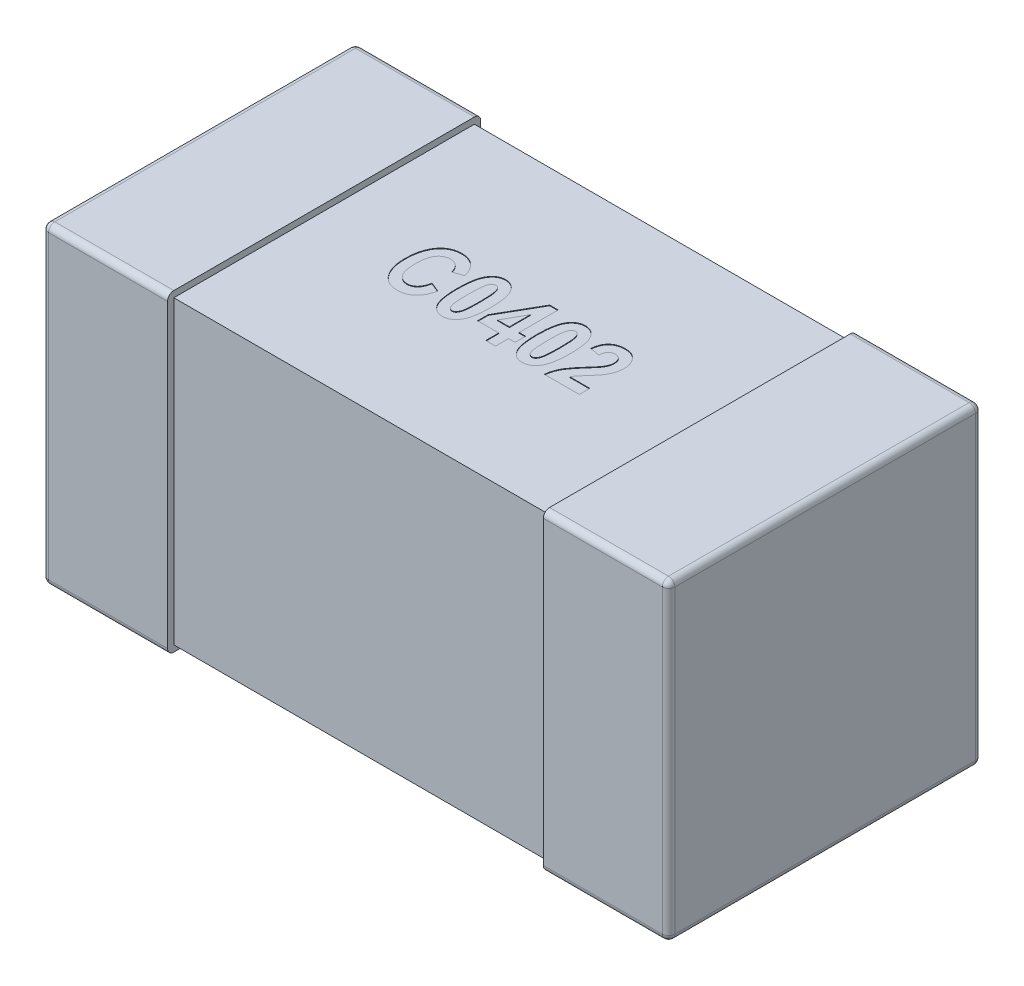
SolidWorks part; units mm, degrees
ref_plane "Front Plane" through (0, 0, 0) normal (0, 0, 1) x (1, 0, 0)
ref_plane "Top Plane" through (0, 0, 0) normal (0, 1, 0) x (1, 0, 0)
ref_plane "Right Plane" through (0, 0, 0) normal (1, 0, 0) x (0, 0, -1)
sketch "Sketch1" plane through (0, 0, 0) normal (0, 1, 0) x (1, 0, 0)
  line L0 (0, 0.15) -> (0, -0.15) construction
  line L1 (-0.5, 0) -> (0, 0) construction
  line L3 (-0.5, 0.25) -> (-0.3, 0.25)
  line L4 (-0.5, 0.25) -> (-0.5, -0.25)
  line L5 (-0.5, -0.25) -> (-0.3, -0.25)
  line L6 (-0.3, 0.25) -> (-0.3, -0.25)
  dimension "BANDWIDTH" = 0.2
  dimension "WIDTH" = 0.5
  dimension "LENGTH-HALF" = 0.5
extrude "THICKNESS" add sketch "Sketch1" along normal blind 0.5
fillet "Fillet1" radius 0.01 8 edges at (-0.5, 0, 0) (-0.4, 0, -0.25) (-0.5, 0.25, -0.25) (-0.4, 0, 0.25) (-0.5, 0.25, 0.25) (-0.5, 0.5, 0) (-0.4, 0.5, -0.25) (-0.4, 0.5, 0.25)
sketch "Sketch2" plane through (0, 0, 0) normal (1, 0, 0) x (0, 0, -1)
  line L0 (0, 0.5) -> (0, 0) construction
  line L1 (-0.24, 0.49) -> (0.24, 0.49)
  line L2 (-0.24, 0.49) -> (-0.24, 0.01)
  line L3 (-0.24, 0.01) -> (0.24, 0.01)
  line L4 (0.24, 0.49) -> (0.24, 0.01)
  line L5 (-0.24, 0.5) -> (0.24, 0.5) construction
  line L6 (-0.24, 0) -> (0.24, 0) construction
  line L7 (-0.25, 0.25) -> (0.25, 0.25) construction
  line L8 (-0.25, 0.49) -> (-0.25, 0.01) construction
  line L9 (0.25, 0.49) -> (0.25, 0.01) construction
  dimension "D1" = 0.01
  dimension "D2" = 0.01
extrude "Boss-Extrude2" add sketch "Sketch2" against normal up to surface (0.3 mm away) up to face at (-0.3, 0.25, 0)
mirror "Mirror3" about plane through (0, 0, 0) normal (1, 0, 0) of "THICKNESS", "Fillet1", "Boss-Extrude2"
sketch "Sketch3" plane through (0, 0.49, 0) normal (0, 1, 0) x (1, 0, 0)
  line L0 (-0.175, -0.05) -> (0.175, -0.05) construction
  line L1 (0, -0.275) -> (0, 0.275) construction
  line L2 (-0.275, 0) -> (0.275, 0) construction
  text T0 "<b>C0402</b>" font "Arial Narrow" height 0.1
  point P2 (0, -0.05)
  dimension "D1" = 0.35
  dimension "D2" = 0.05
extrude "Cut-Extrude1" cut sketch "Sketch3" against normal blind 0.001
